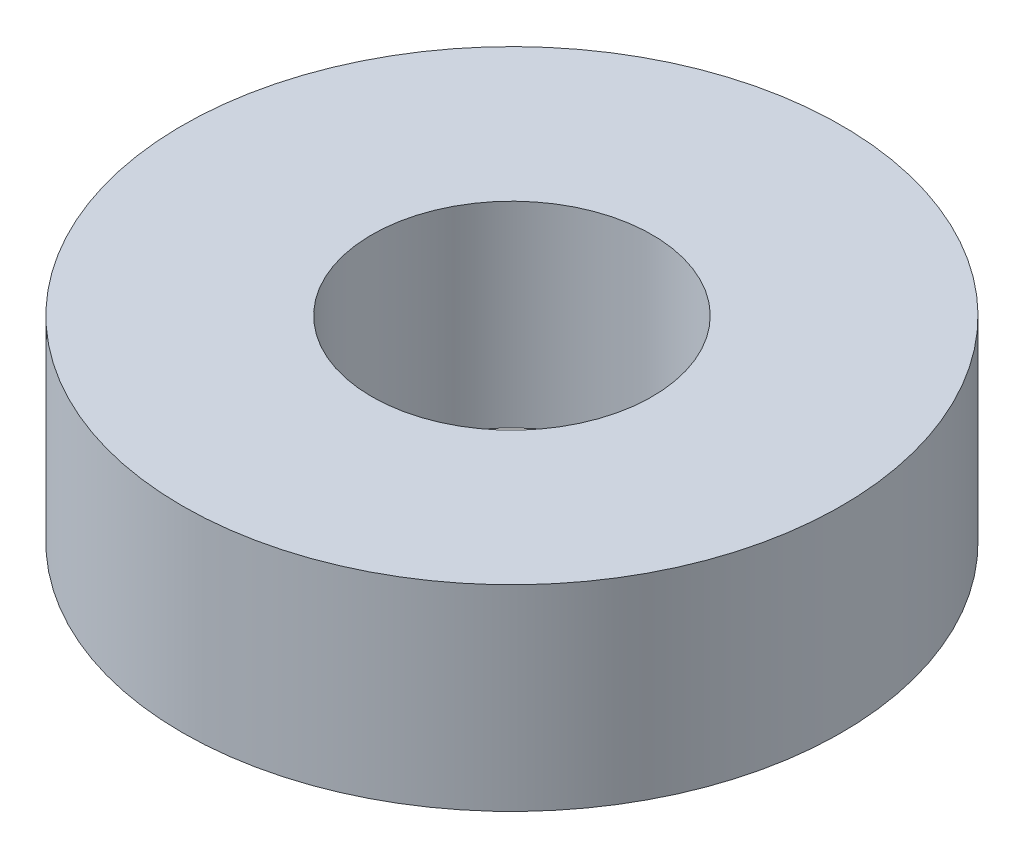
SolidWorks part; units mm, degrees
material "6061 Alloy"
ref_plane "Front Plane" through (0, 0, 0) normal (0, 0, 1) x (1, 0, 0)
ref_plane "Top Plane" through (0, 0, 0) normal (0, 1, 0) x (1, 0, 0)
ref_plane "Right Plane" through (0, 0, 0) normal (1, 0, 0) x (0, 0, -1)
sketch "Sketch1" plane through (0, 0, 0) normal (0, 1, 0) x (1, 0, 0)
  circle A0 centre (0, 0) radius 23.5
  circle A1 centre (0, 0) radius 10
  dimension "D1" = 47
  dimension "D2" = 20
extrude "Boss-Extrude1" add sketch "Sketch1" along normal blind 14 contours A0 | A1
